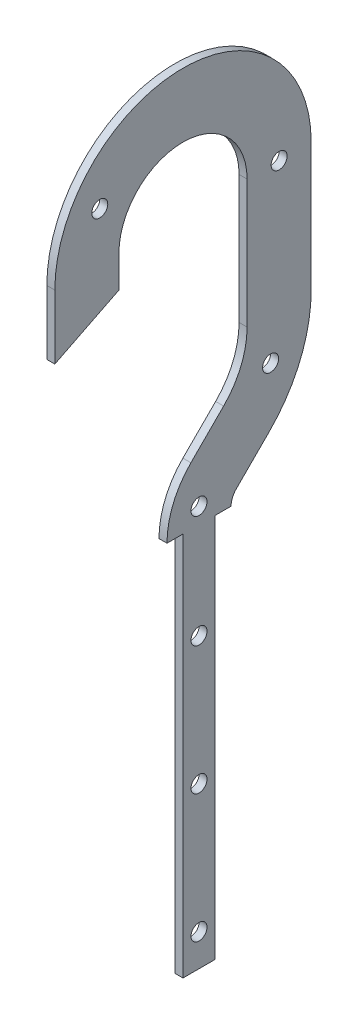
SolidWorks part; units mm, degrees
ref_plane "Front Plane" through (0, 0, 0) normal (0, 0, 1) x (1, 0, 0)
ref_plane "Top Plane" through (0, 0, 0) normal (0, 1, 0) x (1, 0, 0)
ref_plane "Right Plane" through (0, 0, 0) normal (1, 0, 0) x (0, 0, -1)
sketch "Sketch1" plane through (0, 0, 0) normal (1, 0, 0) x (0, 0, -1)
  line L0 (-50.8, 0) -> (-50.8, -25.4)
  line L2 (25.4, 0) -> (25.4, -50.8)
  line L4 (50.8, -50.8) -> (50.8, 0)
  line L5 (-6.35, 0) -> (-6.35, -103.13) construction
  line L6 (6.35, 0) -> (6.35, -103.13) construction
  line L7 (16.1006, -73.2506) -> (3.1306, -86.2206)
  line L8 (3.1306, -86.2206) -> (42.7043, -125.7943) construction
  line L9 (-25.4, 0) -> (-25.4, -12.7)
  line L10 (-50.8, -25.4) -> (-25.4, -12.7)
  line L11 (34.0612, -91.2112) -> (21.0911, -104.1812)
  line L12 (-6.35, -109.1089) -> (0, -109.1089)
  line L13 (0, -109.1089) -> (0, -261.5089)
  line L14 (0, -261.5089) -> (12.7, -261.5089)
  line L15 (12.7, -261.5089) -> (12.7, -109.1089)
  line L16 (12.7, -109.1089) -> (19.05, -109.1089)
  arc A0 (50.8, 0) -> (-50.8, 0) centre (0, 0) ccw
  arc A1 (25.4, 0) -> (-25.4, 0) centre (0, 0) ccw
  arc A2 (25.4, -50.8) -> (16.1006, -73.2506) centre (-6.35, -50.8) cw
  arc A3 (3.1306, -86.2206) -> (-6.35, -109.1089) centre (26.0189, -109.1089) ccw
  arc A4 (50.8, -50.8) -> (34.0612, -91.2112) centre (-6.35, -50.8) cw
  arc A5 (21.0911, -104.1812) -> (19.05, -109.1089) centre (26.0189, -109.1089) ccw
  dimension "D1" = 50.8
  dimension "D3" = 25.4
  dimension "D5" = 6.35
  dimension "D6" = 6.35
  dimension "D7" = 45
  dimension "D9" = 45
  dimension "D8" = 45
  dimension "D2" = 25.4
  dimension "D4" = 50.8
  dimension "D10" = 152.4
  dimension "D11" = 12.7
extrude "Boss-Extrude1" add sketch "Sketch1" along normal blind 3.175
sketch "Sketch2" plane through (3.175, 0, 0) normal (1, 0, 0) x (0, 0, -1)
  line L0 (25.4, 0) -> (25.4, -50.8) construction
  line L1 (22.9832, -62.9502) -> (55.7935, -76.5407) construction
  line L2 (-6.35, -109.1089) -> (0, -109.1089) construction
  line L3 (0, -261.5089) -> (12.7, -261.5089) construction
  circle A0 centre (38.1, 0) radius 3.175
  circle A1 centre (-32.9956, 19.05) radius 3.175
  arc A2 (38.1, 0) -> (-32.9956, 19.05) centre (0, 0) ccw construction
  circle A3 centre (34.7164, -67.8103) radius 3.175
  arc A4 (16.1006, -73.2506) -> (25.4, -50.8) centre (-6.35, -50.8) ccw construction
  circle A5 centre (6.35, -102.7589) radius 3.175
  circle A6 centre (6.35, -248.8089) radius 3.175
  circle A7 centre (6.35, -198.0089) radius 3.175
  circle A8 centre (6.35, -147.2089) radius 3.175
  point P23 (6.35, -261.5089)
  dimension "D1" = 6.35
  dimension "D3" = 6.35
  dimension "D5" = 6.35
  dimension "D7" = 6.35
  dimension "D9" = 6.35
  dimension "D2" = 12.7
  dimension "D4" = 150
  dimension "D6" = 12.7
  dimension "D8" = 6.35
  dimension "D10" = 12.7
  dimension "D11" = 3
extrude "Cut-Extrude1" cut sketch "Sketch2" against normal through all
